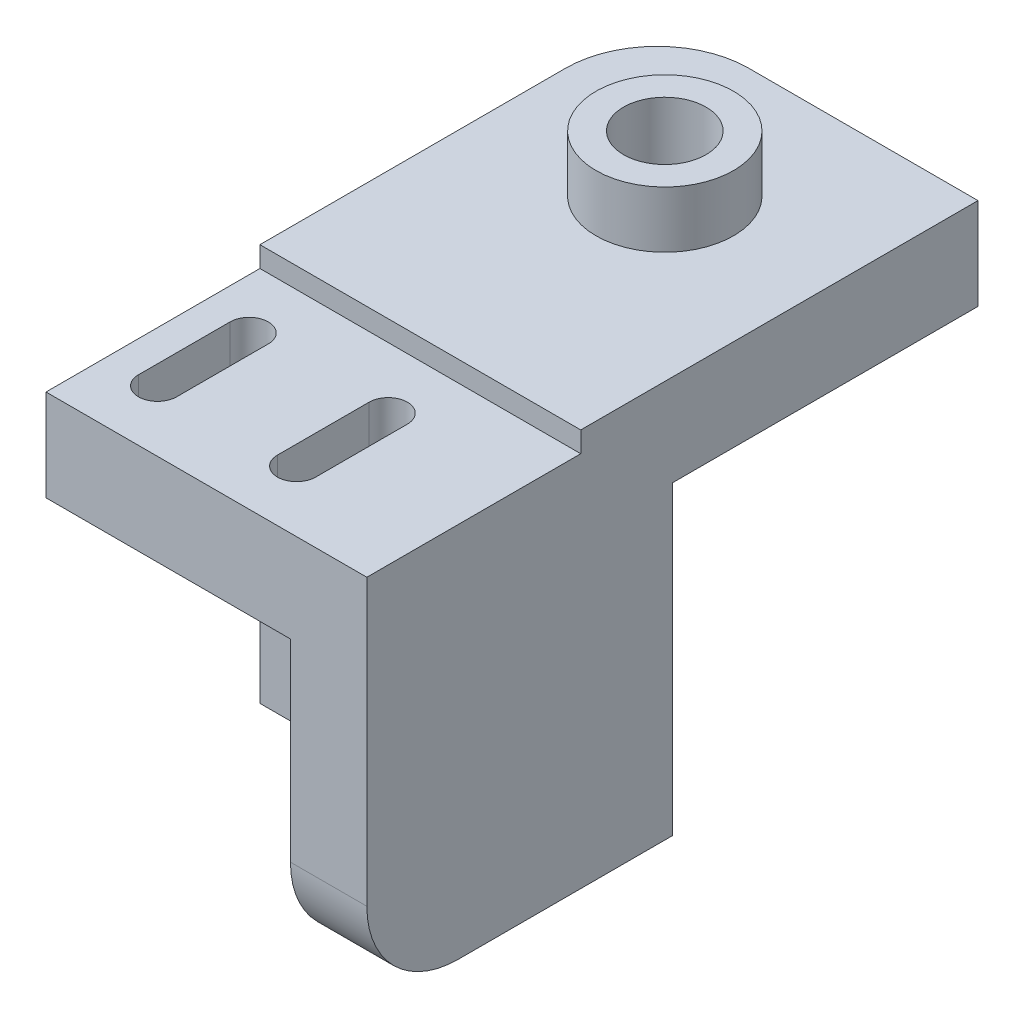
SolidWorks part; units mm, degrees
ref_plane "Płaszczyzna przednia" through (0, 0, 0) normal (0, 0, 1) x (1, 0, 0)
ref_plane "Płaszczyzna górna" through (0, 0, 0) normal (0, 1, 0) x (1, 0, 0)
ref_plane "Płaszczyzna prawa" through (0, 0, 0) normal (1, 0, 0) x (0, 0, -1)
sketch "Szkic1" plane through (0, 0, 0) normal (0, 0, 1) x (1, 0, 0)
  line L1 (0, 0) -> (21, 0)
  line L2 (0, 0) -> (0, 20)
  line L3 (0, 20) -> (21, 20)
  line L4 (21, 0) -> (21, 20)
  line L5 (0, 20) -> (21, 20)
  line L6 (0, 20) -> (0, 26)
  line L7 (0, 26) -> (21, 26)
  line L8 (21, 20) -> (21, 26)
  circle A0 centre (8, 10) radius 2.7
  dimension "D3" = 5.4
  dimension "D1" = 20
  dimension "D2" = 21
  dimension "D4" = 10
  dimension "D5" = 13
  dimension "D6" = 6
extrude "Dodanie-wyciągnięcie1" add sketch "Szkic1" along normal blind 6 contours L3 L8 L7 L6 | L1 L4 L3 L2 A0
sketch "Szkic2" plane through (0, 0, 0) normal (0, 0, -1) x (-1, 0, 0)
  line L0 (0, 0) -> (0, 26) construction
  line L1 (-21, 26) -> (0, 26)
  line L2 (-21, 26) -> (-21, 20)
  line L3 (-21, 20) -> (0, 20)
  line L4 (0, 26) -> (0, 20)
  dimension "D1" = 6
extrude "Dodanie-wyciągnięcie2" add sketch "Szkic2" along normal blind 20
sketch "Szkic3" plane through (0, 26, 0) normal (0, 1, 0) x (1, 0, 0)
  line L0 (0, -6) -> (0, 20) construction
  line L2 (0, 20) -> (21, 20) construction
  circle A0 centre (10.5, 10) radius 2.7
  dimension "D3" = 5.4
  dimension "D1" = 10.5
  dimension "D2" = 10
extrude "Wytnij-wyciągnięcie1" cut sketch "Szkic3" against normal blind 9
sketch "Szkic4" plane through (0, 0, 6) normal (0, 0, 1) x (1, 0, 0)
  line L0 (0, 0) -> (0, 26) construction
  line L1 (0, 18.65) -> (21, 18.65)
  line L2 (0, 18.65) -> (0, 24.65)
  line L3 (0, 24.65) -> (21, 24.65)
  line L4 (21, 18.65) -> (21, 24.65)
  line L5 (21, 0) -> (21, 26) construction
  dimension "D1" = 24.65
  dimension "D2" = 6
extrude "Dodanie-wyciągnięcie3" add sketch "Szkic4" along normal blind 14
sketch "Szkic5" plane through (0, 24.65, 0) normal (0, 1, 0) x (1, 0, 0)
  line L0 (3.3, -16) -> (3.3, -10) construction
  line L1 (2.05, -16) -> (2.05, -10)
  line L2 (4.55, -16) -> (4.55, -10)
  line L3 (0, -20) -> (0, -6) construction
  line L5 (7.85, -6) -> (7.85, -20) construction
  line L6 (21, -6) -> (0, -6) construction
  line L7 (21, -20) -> (0, -20) construction
  line L8 (12.4, -16) -> (12.4, -10) construction
  line L9 (13.65, -16) -> (13.65, -10)
  line L10 (11.15, -16) -> (11.15, -10)
  arc A0 (2.05, -16) -> (4.55, -16) centre (3.3, -16) ccw
  arc A1 (4.55, -10) -> (2.05, -10) centre (3.3, -10) ccw
  arc A2 (13.65, -16) -> (11.15, -16) centre (12.4, -16) cw
  arc A3 (11.15, -10) -> (13.65, -10) centre (12.4, -10) cw
  point P2 (3.3, -13)
  point P18 (12.4, -13)
  dimension "D2" = 2.05
  dimension "D4" = 4
  dimension "D1" = 6
  dimension "D3" = 2.5
  dimension "D5" = 3.3
extrude "Wytnij-wyciągnięcie2" cut sketch "Szkic5" against normal blind 40.05
sketch "Szkic6" plane through (0, 26, 0) normal (0, 1, 0) x (1, 0, 0)
  circle A0 centre (10.5, 10) radius 2.7
  circle A1 centre (10.5, 10) radius 4.5
  dimension "D1" = 5.4
  dimension "D2" = 9
extrude "Dodanie-wyciągnięcie5" add sketch "Szkic6" along normal blind 3.7
fillet "Zaokrąglenie2" radius 6 1 edges at (0, 23, -20)
sketch "Szkic7" plane through (0, 0, 6) normal (0, 0, 1) x (1, 0, 0)
  line L0 (0, 18.65) -> (21, 18.65) construction
  line L1 (21, 0) -> (16, 0)
  line L2 (21, 0) -> (21, 18.65)
  line L3 (21, 18.65) -> (16, 18.65)
  line L4 (16, 0) -> (16, 18.65)
  dimension "D1" = 5
extrude "Dodanie-wyciągnięcie6" add sketch "Szkic7" along normal blind 14
fillet "Zaokrąglenie3" radius 6 1 edges at (18.5, 0, 20)
